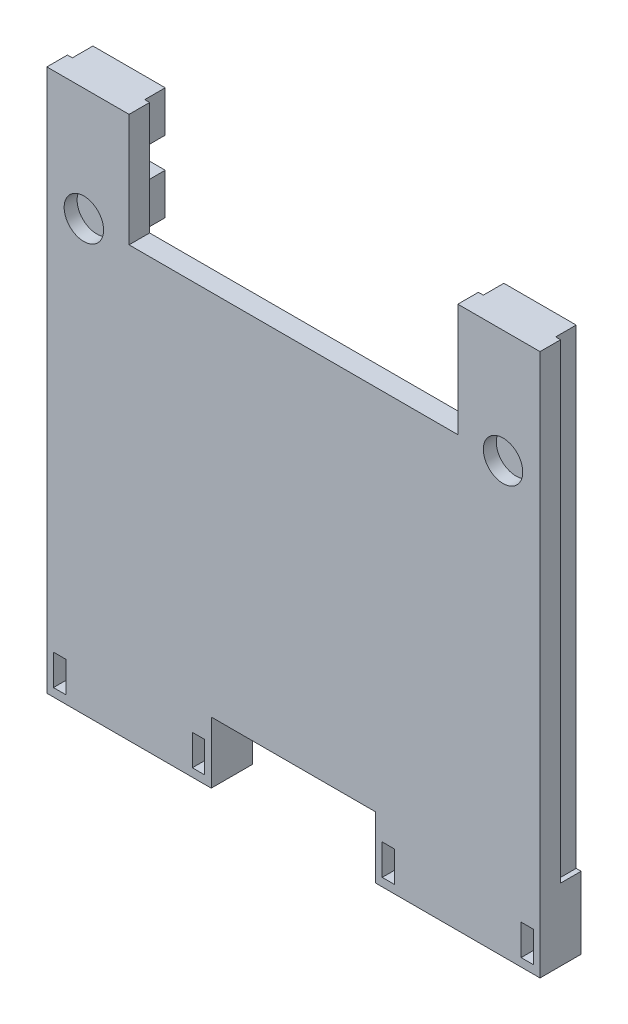
SolidWorks part; units mm, degrees
ref_plane "Front Plane" through (0, 0, 0) normal (0, 0, 1) x (1, 0, 0)
ref_plane "Top Plane" through (0, 0, 0) normal (0, 1, 0) x (1, 0, 0)
ref_plane "Right Plane" through (0, 0, 0) normal (1, 0, 0) x (0, 0, -1)
sketch "Sketch1" plane through (0, 0, 0) normal (0, 0, 1) x (1, 0, 0)
  line L0 (88.9, -120.65) -> (88.9, -36.83)
  line L2 (88.9, -36.83) -> (76.2, -36.83)
  line L3 (12.7, -35.2425) -> (12.7, -120.65) construction
  line L4 (76.2, -36.83) -> (76.2, -54.2925)
  line L5 (76.2, -54.2925) -> (25.4, -54.2925)
  line L6 (25.4, -35.2425) -> (12.7, -35.2425) construction
  line L7 (88.9, -120.65) -> (88.9, -35.2425) construction
  line L8 (25.4, -54.2925) -> (25.4, -36.83)
  line L9 (25.4, -36.83) -> (12.7, -36.83)
  line L10 (76.2, -27.305) -> (76.2, -52.705) construction
  line L11 (12.7, -36.83) -> (12.7, -120.65)
  line L12 (12.7, -120.65) -> (88.9, -120.65) construction
  line L13 (12.7, -120.65) -> (38.1, -120.65)
  line L14 (38.1, -120.65) -> (38.1, -111.125)
  line L15 (38.1, -111.125) -> (63.5, -111.125)
  line L16 (63.5, -111.125) -> (63.5, -120.65)
  line L17 (63.5, -120.65) -> (88.9, -120.65)
  line L18 (25.4, -27.305) -> (25.4, -52.705) construction
  line L25 (44.45, -52.705) -> (25.4, -52.705) construction
  line L26 (38.1, -112.7125) -> (63.5, -112.7125) construction
  dimension "D1" = 1.5875
  dimension "D2" = 1.5875
  dimension "D3" = 1.5875
extrude "base" add sketch "Sketch1" against normal blind 3.175
sketch "Sketch2" plane through (0, 0, -3.175) normal (0, 0, -1) x (-1, 0, 0)
  line L0 (-12.7, -36.83) -> (-12.7, -120.65) construction
  line L1 (-88.9, -120.65) -> (-12.7, -120.65) construction
  line L2 (-88.9, -120.65) -> (-88.9, -109.5375)
  line L3 (-88.9, -109.5375) -> (-12.7, -109.5375) construction
  line L4 (-12.7, -120.65) -> (-12.7, -109.5375)
  line L5 (-25.4, -36.83) -> (-12.7, -36.83) construction
  line L6 (-13.462, -109.5375) -> (-12.7, -109.5375)
  line L7 (-24.638, -87.3125) -> (-16.256, -87.3125)
  line L8 (-63.5, -120.65) -> (-88.9, -120.65) construction
  line L9 (-63.5, -120.65) -> (-88.9, -120.65) construction
  line L10 (-16.256, -87.3125) -> (-16.256, -109.5375)
  line L11 (-16.256, -43.18) -> (-16.256, -80.9625) construction
  line L12 (-24.638, -87.3125) -> (-24.638, -80.9625)
  line L13 (-12.7, -120.65) -> (-38.1, -120.65)
  line L14 (-16.637, -88.9) -> (-16.637, -107.95) construction
  line L15 (-13.462, -36.83) -> (-24.638, -36.83) construction
  line L16 (-13.462, -36.83) -> (-13.462, -109.5375)
  line L17 (-25.4, -88.9) -> (-16.637, -88.9) construction
  line L18 (-16.256, -43.18) -> (-24.638, -43.18)
  line L19 (-16.256, -80.9625) -> (-24.638, -80.9625)
  line L20 (-16.256, -80.9625) -> (-16.256, -76.2794)
  line L21 (-24.638, -36.83) -> (-24.638, -87.3125) construction
  line L22 (-16.256, -76.2794) -> (-24.638, -76.2794)
  line L23 (-24.638, -69.9294) -> (-16.256, -69.9294)
  line L24 (-16.256, -69.9294) -> (-16.256, -65.2462)
  line L25 (-16.256, -65.2462) -> (-24.638, -65.2462)
  line L26 (-24.638, -58.8962) -> (-16.256, -58.8962)
  line L28 (-50.8, -54.2925) -> (-50.8, -109.5375) construction
  line L29 (-16.256, -58.8962) -> (-16.256, -54.2131)
  line L30 (-16.256, -54.2131) -> (-24.638, -54.2131)
  line L31 (-24.638, -47.8631) -> (-16.256, -47.8631)
  line L32 (-16.256, -47.8631) -> (-16.256, -43.18)
  line L33 (-76.2, -54.2925) -> (-25.4, -54.2925) construction
  line L34 (-88.138, -109.5375) -> (-88.9, -109.5375)
  line L35 (-76.962, -36.83) -> (-76.962, -87.3125) construction
  line L36 (-88.138, -36.83) -> (-76.962, -36.83) construction
  line L37 (-85.344, -43.18) -> (-85.344, -80.9625) construction
  line L38 (-76.962, -43.18) -> (-76.962, -36.83)
  line L39 (-88.138, -36.83) -> (-76.962, -36.83)
  line L40 (-76.962, -54.2131) -> (-76.962, -47.8631)
  line L41 (-76.962, -65.2462) -> (-76.962, -58.8962)
  line L42 (-24.638, -76.2794) -> (-24.638, -69.9294)
  line L43 (-76.962, -76.2794) -> (-76.962, -69.9294)
  line L44 (-85.344, -47.8631) -> (-85.344, -43.18)
  line L45 (-76.962, -47.8631) -> (-85.344, -47.8631)
  line L46 (-85.344, -54.2131) -> (-76.962, -54.2131)
  line L47 (-85.344, -58.8962) -> (-85.344, -54.2131)
  line L48 (-76.962, -58.8962) -> (-85.344, -58.8962)
  line L49 (-85.344, -65.2462) -> (-76.962, -65.2462)
  line L50 (-85.344, -69.9294) -> (-85.344, -65.2462)
  line L51 (-76.962, -69.9294) -> (-85.344, -69.9294)
  line L52 (-85.344, -76.2794) -> (-76.962, -76.2794)
  line L53 (-85.344, -80.9625) -> (-85.344, -76.2794)
  line L54 (-85.344, -80.9625) -> (-76.962, -80.9625)
  line L55 (-85.344, -43.18) -> (-76.962, -43.18)
  line L56 (-24.638, -65.2462) -> (-24.638, -58.8962)
  line L57 (-88.138, -36.83) -> (-88.138, -109.5375)
  line L58 (-76.962, -87.3125) -> (-76.962, -80.9625)
  line L59 (-85.344, -87.3125) -> (-85.344, -109.5375)
  line L60 (-76.962, -87.3125) -> (-85.344, -87.3125)
  line L61 (-16.256, -109.5375) -> (-85.344, -109.5375)
  line L62 (-25.4, -54.2925) -> (-25.4, -36.83) construction
  line L70 (-24.638, -54.2131) -> (-24.638, -47.8631)
  line L82 (-38.1, -120.65) -> (-38.1, -111.125)
  line L83 (-38.1, -120.65) -> (-38.1, -111.125) construction
  line L84 (-38.1, -111.125) -> (-63.5, -111.125)
  line L85 (-63.5, -111.125) -> (-63.5, -120.65) construction
  line L86 (-63.5, -111.125) -> (-63.5, -120.65)
  line L87 (-63.5, -120.65) -> (-88.9, -120.65)
  line L88 (-38.1, -111.125) -> (-63.5, -111.125) construction
  line L89 (-12.7, -36.83) -> (-12.7, -120.65) construction
  line L91 (-13.462, -36.83) -> (-24.638, -36.83)
  line L92 (-24.638, -43.18) -> (-24.638, -36.83)
  line L120 (-24.638, -32.1469) -> (-24.638, -25.7969) [skipped]
  dimension "D2" = 0.762
  dimension "D3" = 0.762
  dimension "D4" = 0.381
  dimension "D5" = 2.794
  dimension "D6" = 1.5875
  dimension "D7" = 1.5875
  dimension "D8" = 6.35
  dimension "D11" = 6
extrude "second layer" add sketch "Sketch2" along normal blind 3.175
ref_plane "Plane2" through (50.8, 0, 0) normal (-1, 0, 0) x (0, 0, 1)
sketch "Sketch6" plane through (0, 0, 0) normal (0, 0, 1) x (1, 0, 0)
  line L0 (50.8, -111.125) -> (50.8, -54.2925) construction
  line L1 (38.1, -111.125) -> (63.5, -111.125) construction
  line L2 (76.2, -54.2925) -> (25.4, -54.2925) construction
  line L3 (12.7, -36.83) -> (12.7, -120.65) construction
  line L4 (18.415, -54.2925) -> (25.4, -54.2925) construction
  circle A0 centre (18.415, -54.2925) radius 3.048
  circle A1 centre (83.185, -54.2925) radius 3.048
  dimension "D1" = 6.096
  dimension "D2" = 5.715
extrude "magnet holder" cut sketch "Sketch6" against normal blind 2
sketch "Sketch7" plane through (0, 0, 0) normal (0, 0, 1) x (1, 0, 0)
  line L0 (12.7, -36.83) -> (12.7, -120.65) construction
  line L1 (15.621, -119.38) -> (13.716, -119.38)
  line L2 (15.621, -119.38) -> (15.621, -114.6327)
  line L3 (15.621, -114.6327) -> (13.716, -114.6327)
  line L4 (13.716, -119.38) -> (13.716, -114.6327)
  line L6 (50.8, -111.125) -> (50.8, -54.2925) construction
  line L7 (76.2, -54.2925) -> (25.4, -54.2925) construction
  line L8 (25.4, -120.65) -> (25.4, -74.7109) construction
  line L9 (38.1, -120.65) -> (12.7, -120.65) construction
  line L10 (37.084, -119.38) -> (37.084, -114.6327)
  line L11 (35.179, -114.6327) -> (37.084, -114.6327)
  line L12 (38.1, -111.125) -> (63.5, -111.125) construction
  line L13 (12.7, -120.65) -> (38.1, -120.65) construction
  line L14 (35.179, -119.38) -> (35.179, -114.6327)
  line L15 (35.179, -119.38) -> (37.084, -119.38)
  line L16 (66.421, -119.38) -> (64.516, -119.38)
  line L17 (66.421, -119.38) -> (66.421, -114.6327)
  line L18 (66.421, -114.6327) -> (64.516, -114.6327)
  line L19 (64.516, -119.38) -> (64.516, -114.6327)
  line L20 (87.884, -119.38) -> (87.884, -114.6327)
  line L21 (85.979, -114.6327) -> (87.884, -114.6327)
  line L22 (85.979, -119.38) -> (85.979, -114.6327)
  line L23 (85.979, -119.38) -> (87.884, -119.38)
  dimension "D1" = 1.016
  dimension "D2" = 1.27
  dimension "D3" = 1.905
  dimension "D4" = 4.7473
extrude "small magnets cut" cut sketch "Sketch7" against normal blind 6.35
